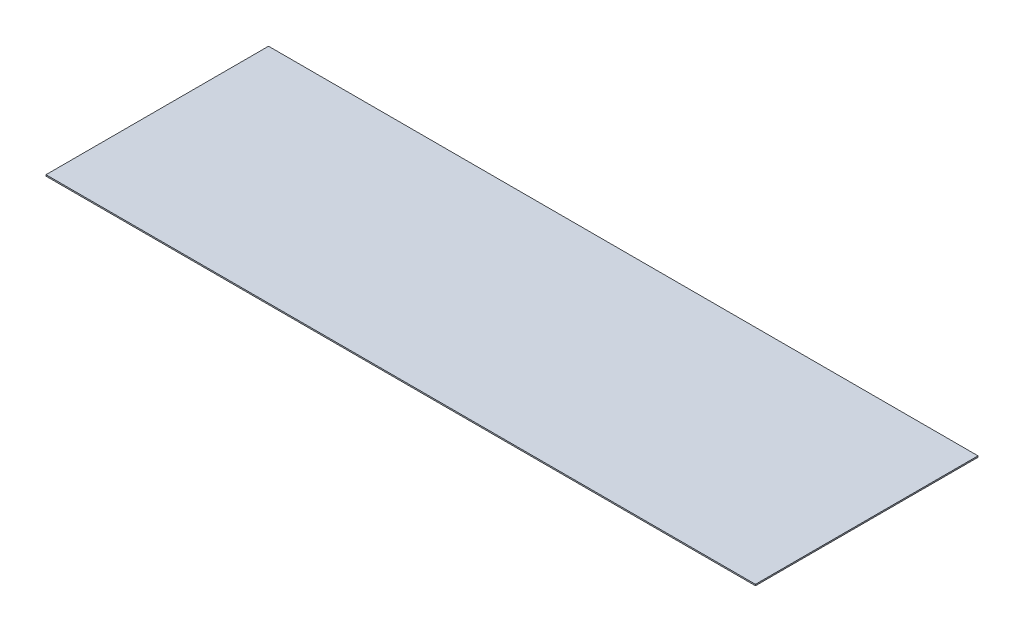
SolidWorks part; units mm, degrees
ref_plane "Front Plane" through (0, 0, 0) normal (0, 0, 1) x (1, 0, 0)
ref_plane "Top Plane" through (0, 0, 0) normal (0, 1, 0) x (1, 0, 0)
ref_plane "Right Plane" through (0, 0, 0) normal (1, 0, 0) x (0, 0, -1)
sketch "Sketch1" plane through (0, 0, 0) normal (0, 1, 0) x (1, 0, 0)
  line L1 (-271, -85) -> (271, -85)
  line L2 (-271, -85) -> (-271, 85)
  line L3 (-271, 85) -> (271, 85)
  line L4 (271, -85) -> (271, 85)
  line L5 (-271, -85) -> (271, 85) construction
  line L6 (-271, 85) -> (271, -85) construction
  point P0 (0, 0)
  dimension "D1" = 170
  dimension "D2" = 542
extrude "Boss-Extrude1" add sketch "Sketch1" along normal blind 1
